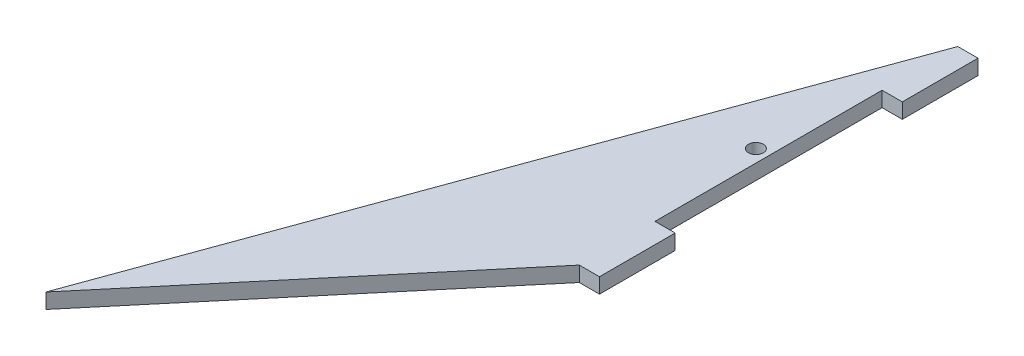
SolidWorks part; units mm, degrees
material "Acrylic (Medium-high impact)"
ref_plane "Front Plane" through (0, 0, 0) normal (0, 0, 1) x (1, 0, 0)
ref_plane "Top Plane" through (0, 0, 0) normal (0, 1, 0) x (1, 0, 0)
ref_plane "Right Plane" through (0, 0, 0) normal (1, 0, 0) x (0, 0, -1)
sketch "Sketch1" plane through (0, 0, 0) normal (0, 1, 0) x (1, 0, 0)
  line L0 (-48.2091, -57.4533) -> (0, 75)
  line L1 (0, 75) -> (0, 0)
  line L2 (0, 0) -> (-48.2091, -57.4533)
  dimension "D1" = 75
  dimension "D2" = 140
  dimension "D3" = 20
extrude "Boss-Extrude1" add sketch "Sketch1" along normal blind 3
sketch "Sketch2" plane through (0, 0, 0) normal (1, 0, 0) x (0, 0, -1)
  line L0 (0, 3) -> (75, 3) construction
  line L1 (0, 0) -> (15, 0)
  line L2 (0, 0) -> (0, 3)
  line L3 (0, 3) -> (15, 3)
  line L4 (15, 0) -> (15, 3)
  line L6 (75, 0) -> (60, 0)
  line L7 (75, 0) -> (75, 3)
  line L8 (75, 3) -> (60, 3)
  line L9 (60, 0) -> (60, 3)
  dimension "D1" = 15
  dimension "D2" = 15
  dimension "D3" = 45
extrude "Boss-Extrude2" add sketch "Sketch2" along normal blind 4
sketch "Sketch3" plane through (0, 3, 0) normal (0, 1, 0) x (1, 0, 0)
  line L0 (0, 37.5) -> (-13.6489, 37.5) construction
  line L1 (0, 15) -> (0, 60) construction
  line L2 (0, 75) -> (-48.2091, -57.4533) construction
  circle A0 centre (-2.5, 37.5) radius 1.4732
  dimension "D1" = 2.9464
  dimension "D2" = 2.5
extrude "Cut-Extrude1" cut sketch "Sketch3" against normal through all
